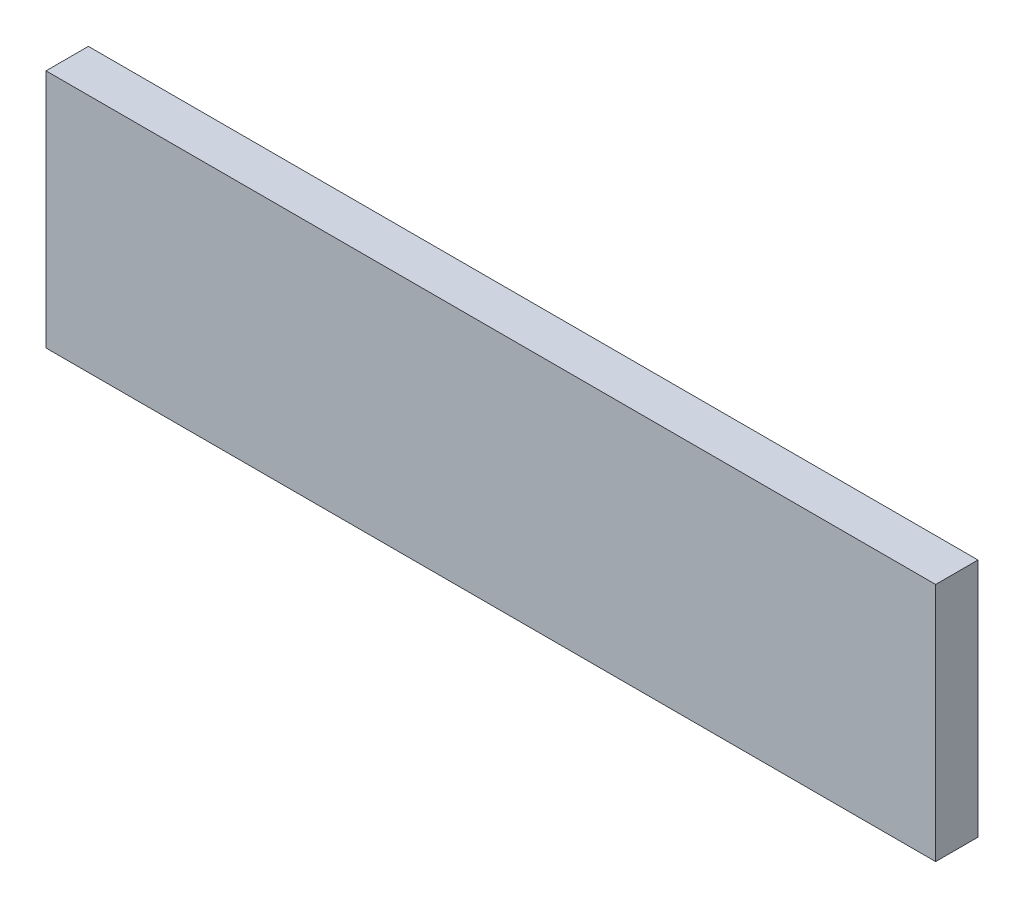
SolidWorks part; units mm, degrees
material "Oak"
ref_plane "Front Plane" through (0, 0, 0) normal (0, 0, 1) x (1, 0, 0)
ref_plane "Top Plane" through (0, 0, 0) normal (0, 1, 0) x (1, 0, 0)
ref_plane "Right Plane" through (0, 0, 0) normal (1, 0, 0) x (0, 0, -1)
sketch "Sketch1" plane through (0, 0, 0) normal (0, 0, 1) x (1, 0, 0)
  line L1 (-200.025, -53.975) -> (200.025, -53.975)
  line L2 (-200.025, -53.975) -> (-200.025, 53.975)
  line L3 (-200.025, 53.975) -> (200.025, 53.975)
  line L4 (200.025, -53.975) -> (200.025, 53.975)
  line L5 (-200.025, -53.975) -> (200.025, 53.975) construction
  line L6 (-200.025, 53.975) -> (200.025, -53.975) construction
  point P0 (0, 0)
  dimension "D1" = 400.05
  dimension "D2" = 107.95
extrude "Boss-Extrude1" add sketch "Sketch1" along normal blind 19.05
